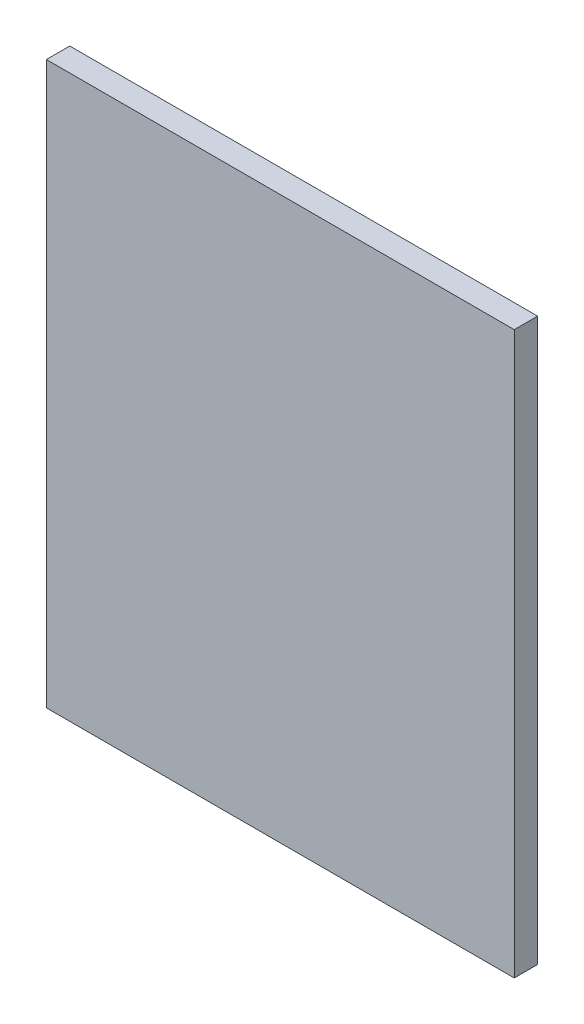
SolidWorks part; units mm, degrees
ref_plane "Front Plane" through (0, 0, 0) normal (0, 0, 1) x (1, 0, 0)
ref_plane "Top Plane" through (0, 0, 0) normal (0, 1, 0) x (1, 0, 0)
ref_plane "Right Plane" through (0, 0, 0) normal (1, 0, 0) x (0, 0, -1)
sketch "Sketch2" plane through (0, 0, 0) normal (0, 0, 1) x (1, 0, 0)
  line L1 (-31.75, -38.1) -> (31.75, -38.1)
  line L2 (-31.75, -38.1) -> (-31.75, 38.1)
  line L3 (-31.75, 38.1) -> (31.75, 38.1)
  line L4 (31.75, -38.1) -> (31.75, 38.1)
  line L5 (-31.75, -38.1) -> (31.75, 38.1) construction
  line L6 (-31.75, 38.1) -> (31.75, -38.1) construction
  point P0 (0, 0)
  dimension "D1" = 63.5
  dimension "D2" = 76.2
extrude "Boss-Extrude1" add sketch "Sketch2" along normal mid plane 3.175
